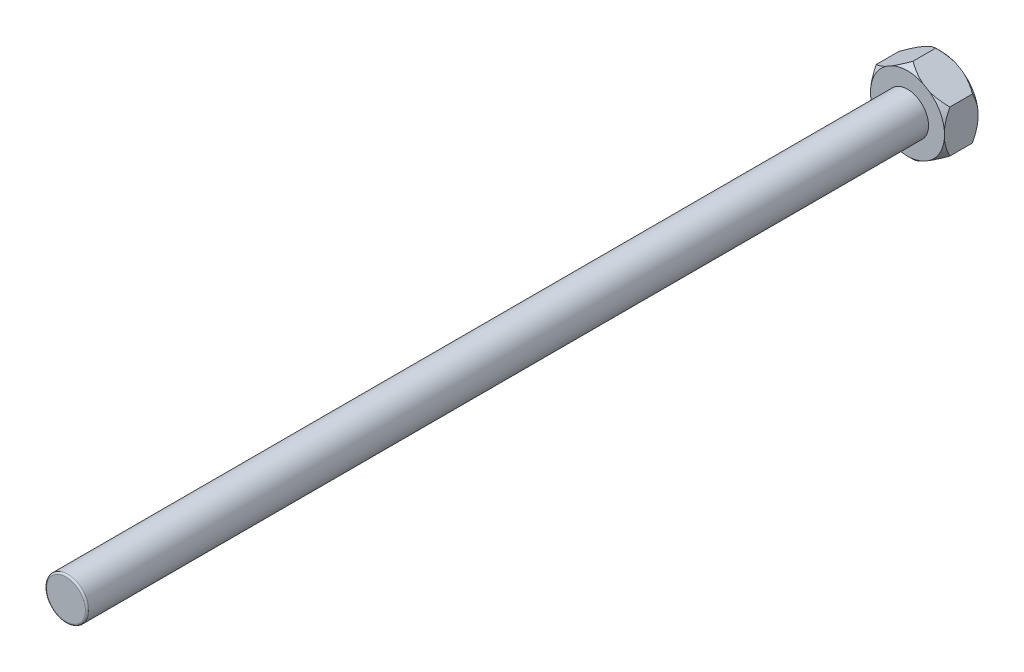
SolidWorks part; units mm, degrees
ref_plane "前视基准面" through (0, 0, 0) normal (0, 0, 1) x (1, 0, 0)
ref_plane "上视基准面" through (0, 0, 0) normal (0, 1, 0) x (1, 0, 0)
ref_plane "右视基准面" through (0, 0, 0) normal (1, 0, 0) x (0, 0, -1)
sketch "草图1" plane through (0, 0, 0) normal (0, 0, 1) x (1, 0, 0)
  line L1 (0, 4.0415) -> (-3.5, 2.0207)
  line L2 (-3.5, 2.0207) -> (-3.5, -2.0207)
  line L3 (-3.5, -2.0207) -> (0, -4.0415)
  line L4 (0, -4.0415) -> (3.5, -2.0207)
  line L5 (3.5, -2.0207) -> (3.5, 2.0207)
  line L6 (3.5, 2.0207) -> (0, 4.0415)
  circle A0 centre (0, 0) radius 3.5 construction
  dimension "D1" = 7
extrude "凸台-拉伸1" add sketch "草图1" against normal blind 3.2
sketch "草图2" plane through (0, 0, 0) normal (0, 0, 1) x (1, 0, 0)
  circle A0 centre (0, 0) radius 2
  dimension "D1" = 4
sketch "草图3" plane through (0, 0, 0) normal (1, 0, 0) x (0, 0, -1)
  line L0 (0, 0) -> (-7.5807, 0) construction
  line L1 (0.523, 4.0415) -> (0, 3.5185)
  line L2 (3.2, 4.0415) -> (0, 4.0415) construction
  line L3 (0, 2.0207) -> (0, 4.0415) construction
  line L4 (0, 3.5185) -> (0, 4.0415)
  line L5 (0, 4.0415) -> (0.523, 4.0415)
  line L6 (3.2, 4.0415) -> (3.2, 3.5185)
  line L7 (3.2, 2.0207) -> (3.2, 4.0415) construction
  line L8 (3.2, 3.5185) -> (2.677, 4.0415)
  line L9 (2.677, 4.0415) -> (3.2, 4.0415)
revolve "切除-旋转1" cut sketch "草图3" angle 360 about L0
extrude "凸台-拉伸2" add sketch "草图2" along normal blind 80
fillet "圆角1" radius 0.16 1 edges at (2, 0, 80)
